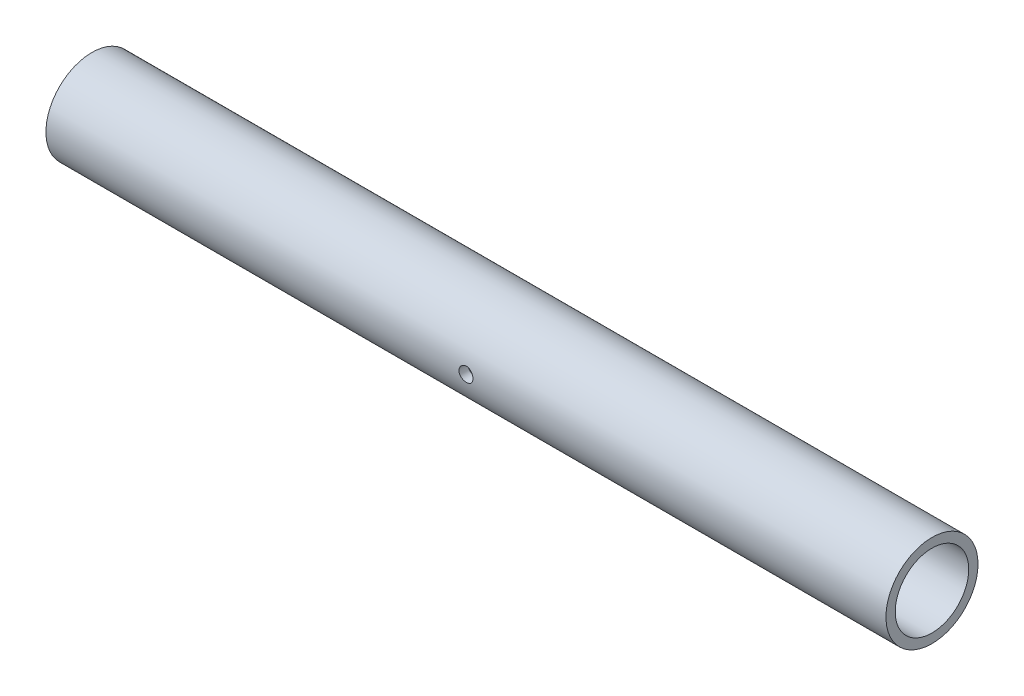
SolidWorks part; units mm, degrees
ref_plane "Front Plane" through (0, 0, 0) normal (0, 0, 1) x (1, 0, 0)
ref_plane "Top Plane" through (0, 0, 0) normal (0, 1, 0) x (1, 0, 0)
ref_plane "Right Plane" through (0, 0, 0) normal (1, 0, 0) x (0, 0, -1)
sketch "Sketch1" plane through (0, 0, 0) normal (1, 0, 0) x (0, 0, -1)
  circle A0 centre (0, 0) radius 16.7005
  circle A1 centre (0, 0) radius 13.335
  dimension "D1" = 33.401
  dimension "D2" = 26.67
extrude "Boss-Extrude1" add sketch "Sketch1" along normal blind 304.8
hole_wizard "1/4-20 Tapped Hole1" positions "3DSketch2" profile "Sketch3" tap size "1/4-20" standard "ANSI Inch"
sketch3d "3DSketch2"
  point P0 (152.4, 0, 16.7005)
sketch "Sketch3" plane through (152.4, 0, 16.7005) normal (1, 0, 0) x (0, -1, 0)
  line L0 (0, 0) -> (0, 3.3655)
  line L1 (0, 3.3655) -> (2.5527, 3.3655)
  line L2 (2.5527, 3.3655) -> (2.5527, 0)
  line L5 (2.5527, 0) -> (0, 0)
  line L11 (0, -6.35) -> (0, 107.95) construction
  dimension "Thru Tap Drill Dia." = 5.1054
  dimension "Thru Tap Drill Depth" = 3.3655
cosmetic thread "Hole Thread1" parameters "D2"=6.35
